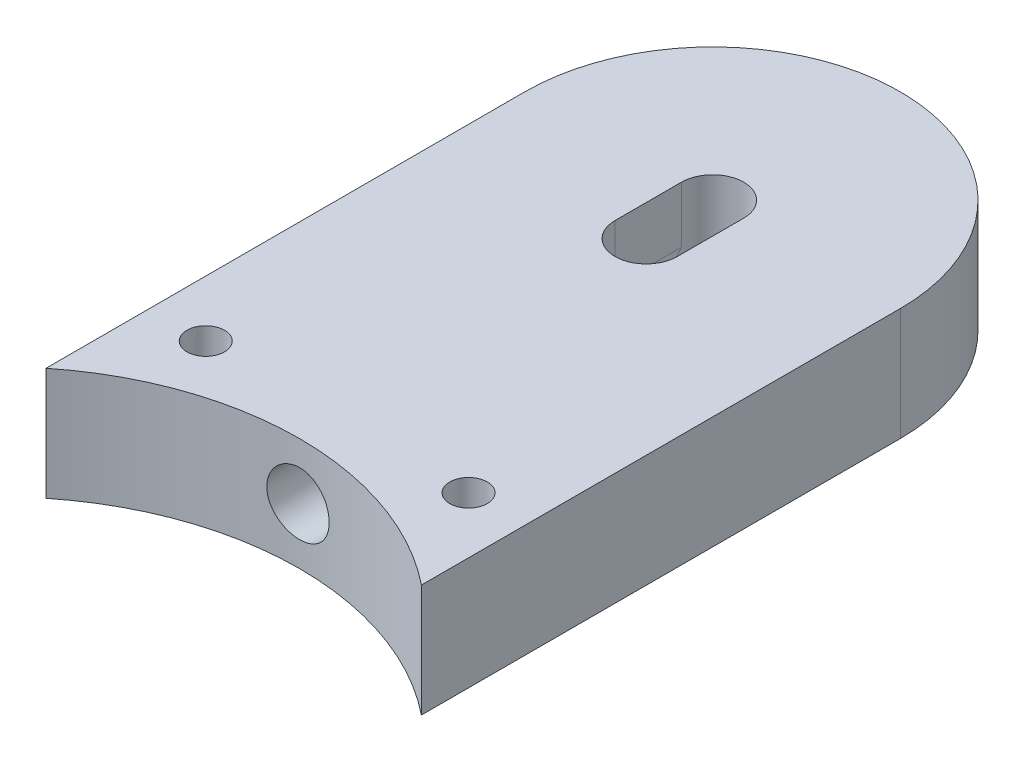
SolidWorks part; units mm, degrees
ref_plane "Plan de face" through (0, 0, 0) normal (0, 0, 1) x (1, 0, 0)
ref_plane "Plan de dessus" through (0, 0, 0) normal (0, 1, 0) x (1, 0, 0)
ref_plane "Plan de droite" through (0, 0, 0) normal (1, 0, 0) x (0, 0, -1)
sketch "Esquisse1" plane through (0, 0, 0) normal (0, 1, 0) x (1, 0, 0)
  line L0 (0, 0) -> (0, 223.7456) construction
  line L1 (25, 31.225) -> (25, 95)
  line L2 (-25, 31.225) -> (-25, 95)
  line L3 (25, 40) -> (-25, 40) construction
  line L4 (25, 120) -> (-25, 120) construction
  line L6 (25, 95) -> (-25, 95) construction
  line L9 (25, 0) -> (25, 223.7456) construction
  line L11 (-25, 0) -> (-25, 223.7456) construction
  arc A0 (25, 31.225) -> (-25, 31.225) centre (0, 0) ccw
  arc A1 (-25, 95) -> (25, 95) centre (0, 95) cw
  circle A2 centre (0, 95) radius 4.15
  dimension "D1" = 40
  dimension "D3" = 80
  dimension "D5" = 25
extrude "Boss.-Extru.1" add sketch "Esquisse1" along normal blind 15
sketch "Esquisse2" plane through (0, 0, 0) normal (0, 0, 1) x (1, 0, 0)
  line L0 (-25, 7.5) -> (25, 7.5) construction
  line L1 (-25, 15) -> (-25, 0) construction
  line L2 (25, 15) -> (25, 0) construction
  line L3 (0, 15) -> (0, 0) construction
  line L4 (25, 15) -> (-25, 15) construction
  circle A0 centre (0, 7.5) radius 4.15
extrude "Enlèv. mat.-Extru.1" cut sketch "Esquisse2" against normal up to next
sketch "Esquisse3" plane through (0, 15, 0) normal (0, 1, 0) x (-1, 0, 0)
  line L0 (4.15, -95) -> (-4.15, -95) construction
  line L1 (4.15, -82) -> (-4.15, -82) construction
  line L2 (4.15, -95) -> (4.15, -86.15)
  line L3 (-4.15, -86.15) -> (-4.15, -95)
  line L4 (4.15, -86.15) -> (-4.15, -86.15) construction
  circle A0 centre (0, -95) radius 4.15 construction
  arc A1 (-4.15, -95) -> (4.15, -95) centre (0, -95) ccw
  arc A3 (4.15, -86.15) -> (-4.15, -86.15) centre (0, -86.15) ccw
  dimension "D2" = 4.15
  dimension "D1" = 13
extrude "Enlèv. mat.-Extru.2" cut sketch "Esquisse3" against normal blind 7.5
hole_wizard "Trou taraudé M6x1.01" positions "Esquisse5" profile "Esquisse4" tap size "M6x1.0" standard "Ansi Metric" end condition through all
sketch "Esquisse5" plane through (0, 0, 0) normal (0, -1, 0) x (1, 0, 0)
  point P0 (17.5, -45)
  point P2 (-17.5, -45)
sketch "Esquisse4" plane through (17.5, 0, -45) normal (1, 0, 0) x (0, 0, -1)
  line L0 (0, 0) -> (0, 15)
  line L1 (0, 15) -> (2.5, 15)
  line L2 (2.5, 15) -> (2.5, 0)
  line L5 (2.5, 0) -> (0, 0)
  line L11 (0, -6.35) -> (0, 107.95) construction
  dimension "Diamètre du trou pour taraudage jusqu'au prochain" = 5
  dimension "Profondeur du trou pour taraudage jusqu'au prochain" = 15
cosmetic thread "Filetage de perçage1" parameters "D2"=6
cosmetic thread "Filetage de perçage2" parameters "D2"=6
